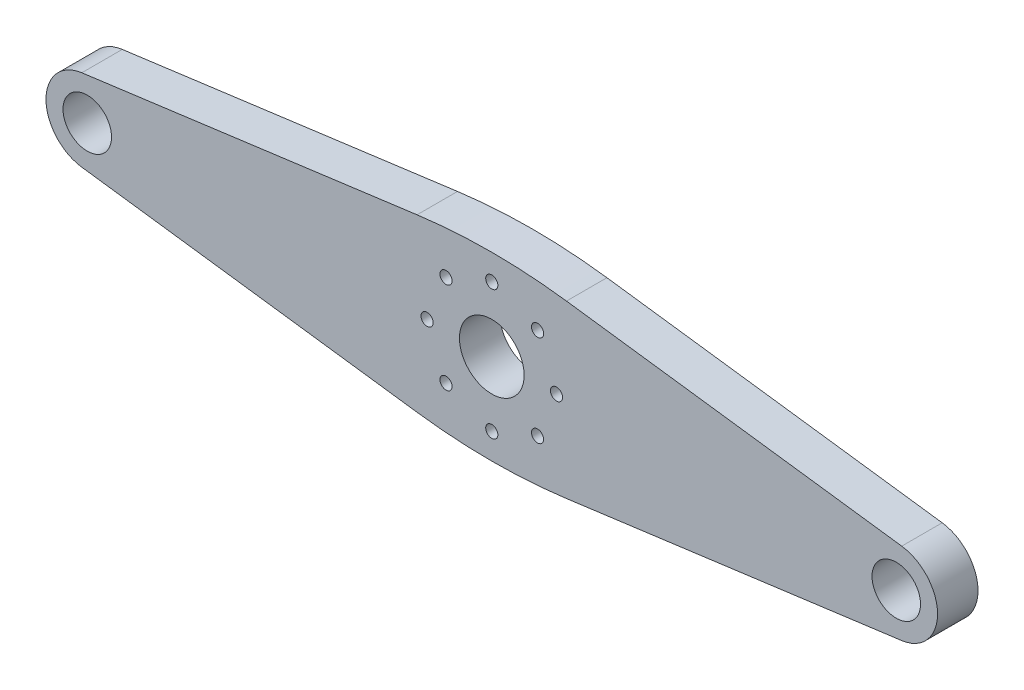
SolidWorks part; units mm, degrees
material "ABS"
ref_plane "Płaszczyzna przednia" through (0, 0, 0) normal (0, 0, 1) x (1, 0, 0)
ref_plane "Płaszczyzna górna" through (0, 0, 0) normal (0, 1, 0) x (1, 0, 0)
ref_plane "Płaszczyzna prawa" through (0, 0, 0) normal (1, 0, 0) x (0, 0, -1)
sketch "Szkic1" plane through (0, 0, 0) normal (0, 0, 1) x (1, 0, 0)
  line L0 (-44.521, 0) -> (57.4684, 0) construction
  line L1 (0, 0) -> (0, 26.3225) construction
  line L2 (-50.6729, 5.0557) -> (-9.2351, 10.5708)
  line L3 (-50.6729, -5.0557) -> (-9.2351, -10.5708)
  line L4 (50.6729, -5.0557) -> (9.2351, -10.5708)
  line L5 (50.6729, 5.0557) -> (9.2351, 10.5708)
  circle A0 centre (0, 0) radius 4
  circle A1 centre (-5.6569, 5.6569) radius 0.75
  circle A2 centre (-8, 0) radius 0.75
  circle A3 centre (0, 8) radius 0.75
  circle A4 centre (5.6569, 5.6569) radius 0.75
  circle A5 centre (-50, 0) radius 3
  circle A6 centre (50, 0) radius 3
  arc A7 (-50.6729, 5.0557) -> (-50.6729, -5.0557) centre (-50, 0) ccw
  arc A8 (50.6729, 5.0557) -> (50.6729, -5.0557) centre (50, 0) cw
  arc A9 (-9.2351, 10.5708) -> (9.2351, 10.5708) centre (0, -58.8174) cw
  arc A10 (-9.2351, -10.5708) -> (9.2351, -10.5708) centre (0, 58.8174) ccw
  circle A11 centre (8, 0) radius 0.75
  circle A12 centre (5.6569, -5.6569) radius 0.75
  circle A13 centre (0, -8) radius 0.75
  circle A14 centre (-5.6569, -5.6569) radius 0.75
  point P16 (0, 0)
  point P28 (0, 11.7999)
  point P31 (0, -11.7999)
  point P34 (0, 0)
  point P42 (0, 0)
  point P47 (0, 0)
  dimension "D1" = 8
  dimension "D2" = 50
  dimension "D3" = 8
  dimension "D4" = 6
  dimension "D5" = 1.5
  dimension "D7" = 70
extrude "Dodanie-wyciągnięcie1" add sketch "Szkic1" along normal blind 5
